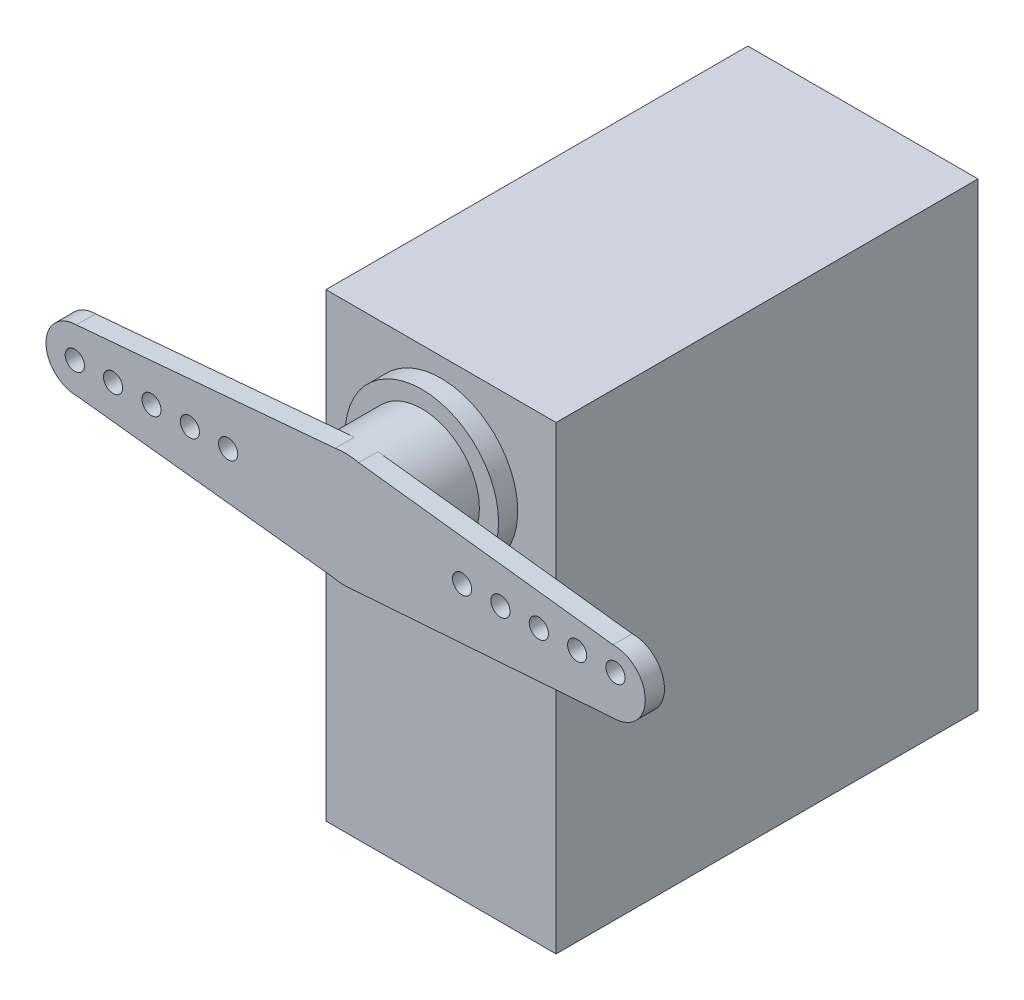
SolidWorks part; units mm, degrees
ref_plane "Front Plane" through (0, 0, 0) normal (0, 0, 1) x (1, 0, 0)
ref_plane "Top Plane" through (0, 0, 0) normal (0, 1, 0) x (1, 0, 0)
ref_plane "Right Plane" through (0, 0, 0) normal (1, 0, 0) x (0, 0, -1)
sketch "Sketch1" plane through (0, 0, 0) normal (0, 0, 1) x (1, 0, 0)
  line L1 (-9.525, -19.05) -> (9.525, -19.05)
  line L2 (-9.525, -19.05) -> (-9.525, 19.05)
  line L3 (-9.525, 19.05) -> (9.525, 19.05)
  line L4 (9.525, -19.05) -> (9.525, 19.05)
  line L5 (-9.525, -19.05) -> (9.525, 19.05) construction
  line L6 (-9.525, 19.05) -> (9.525, -19.05) construction
  point P0 (0, 0)
  dimension "D1" = 19.05
  dimension "D2" = 38.1
extrude "Boss-Extrude1" add sketch "Sketch1" along normal blind 34.925
sketch "Sketch2" plane through (0, 0, 34.925) normal (0, 0, 1) x (1, 0, 0)
  line L0 (9.525, 19.05) -> (-9.525, 19.05) construction
  circle A0 centre (0, 11.1125) radius 6.35
  dimension "D1" = 12.7
  dimension "D2" = 7.9375
extrude "Boss-Extrude2" add sketch "Sketch2" along normal blind 1.5875
sketch "Sketch3" plane through (0, 0, 36.5125) normal (0, 0, 1) x (1, 0, 0)
  circle A0 centre (0, 11.308) radius 4.7625
  dimension "D1" = 9.525
extrude "Boss-Extrude3" add sketch "Sketch3" along normal blind 6.35
sketch "Sketch4" plane through (0, 0, 42.8625) normal (0, 0, 1) x (1, 0, 0)
  line L0 (0, 16.0705) -> (-22.2536, 14.1273)
  line L1 (0, 6.5455) -> (-22.1973, 9.0514)
  line L2 (0, 20.5445) -> (0, -5.3026) construction
  line L3 (0, 16.0705) -> (22.1793, 13.4101)
  line L4 (0, 6.5455) -> (22.2791, 8.1707)
  circle A0 centre (0, 11.308) radius 4.7625 construction
  circle A1 centre (0, 11.308) radius 4.7625 construction
  arc A2 (-22.1973, 9.0514) -> (-22.2536, 14.1273) centre (-22.225, 11.5893) cw
  arc A3 (22.1793, 13.4101) -> (22.2791, 8.1707) centre (22.225, 10.7903) cw
  dimension "D1" = 22.225
  dimension "D2" = 22.225
extrude "Boss-Extrude4" add sketch "Sketch4" against normal blind 1.5875
sketch "Sketch5" plane through (0, 0, 42.8625) normal (0, 0, 1) x (1, 0, 0)
  line L0 (-24.7629, 11.5612) -> (24.8447, 10.8402) construction
  arc A0 (-22.2536, 14.1273) -> (-22.1973, 9.0514) centre (-22.225, 11.5893) ccw construction
  arc A1 (22.2791, 8.1707) -> (22.1793, 13.4101) centre (22.225, 10.7903) ccw construction
  circle A2 centre (-22.3817, 11.5266) radius 0.7937
  dimension "D1" = 1.5875
  dimension "D2" = 2.3813
extrude "Cut-Extrude1" cut sketch "Sketch5" against normal blind 6.35
pattern_linear "LPattern1" count 5 spacing 3.175 along (1, 0, 0) of "Cut-Extrude1"
mirror "Mirror1" about plane through (0, 0, 0) normal (1, 0, 0) of "LPattern1", "Cut-Extrude1"
